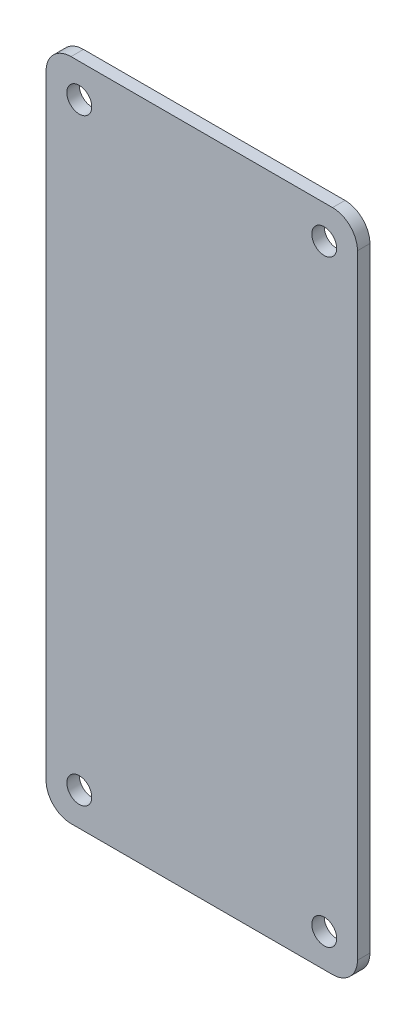
SolidWorks part; units mm, degrees
ref_plane "Alzado" through (0, 0, 0) normal (0, 0, 1) x (1, 0, 0)
ref_plane "Planta" through (0, 0, 0) normal (0, 1, 0) x (1, 0, 0)
ref_plane "Vista lateral" through (0, 0, 0) normal (1, 0, 0) x (0, 0, -1)
sketch "Croquis1" plane through (0, 0, 0) normal (0, 0, 1) x (1, 0, 0)
  line L0 (0, -80) -> (0, 80) construction
  line L1 (37.5, 80) -> (-37.5, 80)
  line L2 (37.5, 80) -> (37.5, -80)
  line L3 (37.5, -80) -> (-37.5, -80)
  line L4 (-37.5, 80) -> (-37.5, -80)
  line L5 (37.5, 80) -> (-37.5, -80) construction
  line L6 (37.5, -80) -> (-37.5, 80) construction
  line L7 (-37.5, 0) -> (37.5, 0) construction
  circle A2 centre (-29.5, 72) radius 3
  circle A3 centre (29.5, 72) radius 3
  circle A4 centre (-29.5, -72) radius 3
  circle A5 centre (29.5, -72) radius 3
  point P0 (0, 0)
  dimension "D5" = 6
  dimension "D1" = 75
  dimension "D2" = 160
  dimension "D6" = 8
  dimension "D7" = 8
extrude "Saliente-Extruir1" add sketch "Croquis1" along normal blind 3
fillet "Redondeo1" radius 6 4 edges at (-37.5, 80, 1.5) (37.5, 80, 1.5) (37.5, -80, 1.5) (-37.5, -80, 1.5)
